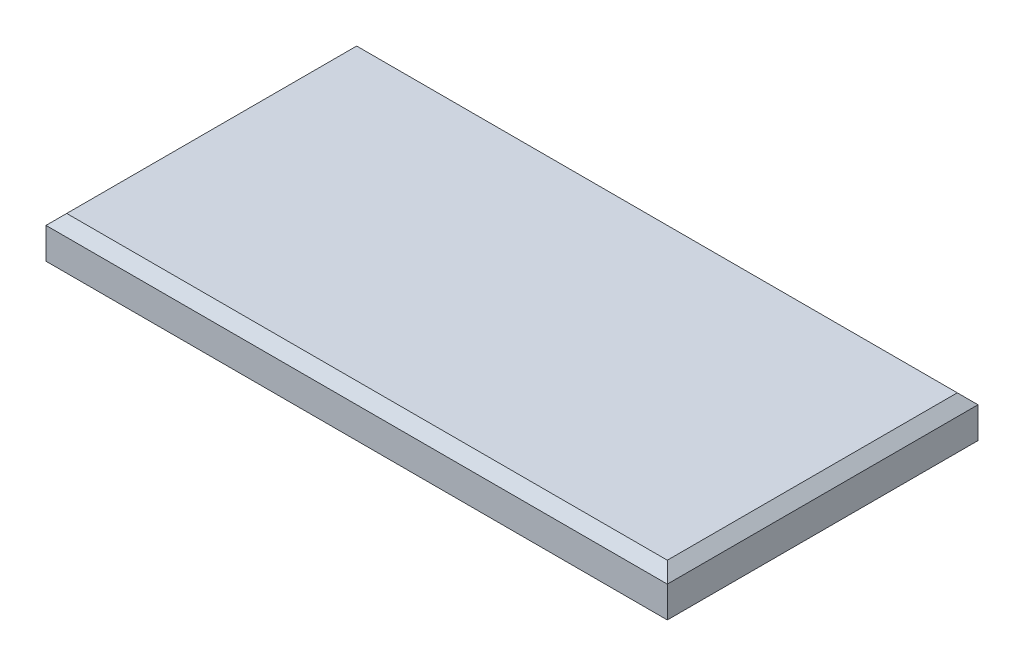
SolidWorks part; units mm, degrees
ref_plane "Front Plane" through (0, 0, 0) normal (0, 0, 1) x (1, 0, 0)
ref_plane "Top Plane" through (0, 0, 0) normal (0, 1, 0) x (1, 0, 0)
ref_plane "Right Plane" through (0, 0, 0) normal (1, 0, 0) x (0, 0, -1)
sketch "Sketch1" plane through (0, 0, 0) normal (0, 1, 0) x (1, 0, 0)
  line L1 (-30, -15) -> (30, -15)
  line L2 (-30, -15) -> (-30, 15)
  line L3 (-30, 15) -> (30, 15)
  line L4 (30, -15) -> (30, 15)
  line L5 (-30, -15) -> (30, 15) construction
  line L6 (-30, 15) -> (30, -15) construction
  point P0 (0, 0)
  dimension "D1" = 30
  dimension "D2" = 60
extrude "Boss-Extrude1" add sketch "Sketch1" along normal blind 4
shell "Shell1" thickness 2
sketch "Sketch2" plane through (0, 2, 0) normal (0, -1, 0) x (1, 0, 0)
  line L0 (0, 0) -> (-27.3454, 0) construction
  line L1 (0, 0) -> (0, 8.2989) construction
  circle A0 centre (-15, 0) radius 2
  circle A1 centre (15, 0) radius 2
  dimension "D1" = 4
  dimension "D2" = 15
extrude "Boss-Extrude2" add sketch "Sketch2" along normal blind 10
fillet "Fillet1" radius 1 2 edges at (15, -8, 2) (-15, -8, -2)
chamfer "Chamfer1" distance 1 angle 45 4 edges at (0, 4, 15) (-30, 4, 0) (0, 4, -15) (30, 4, 0)
